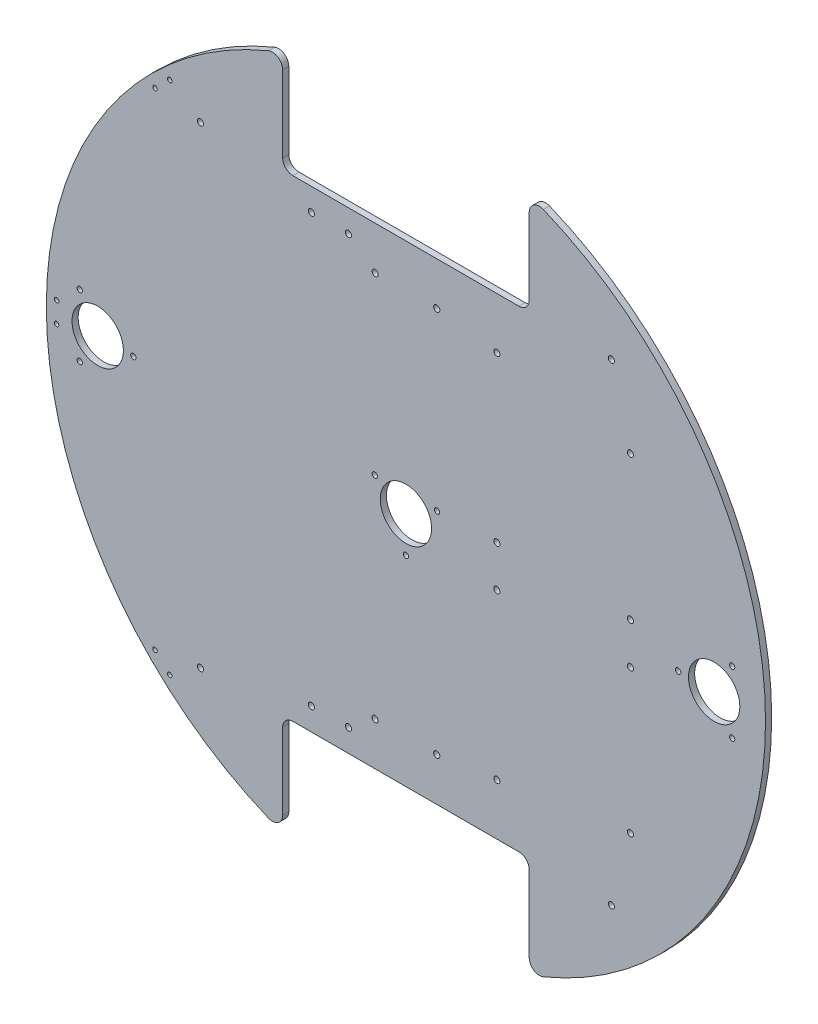
SolidWorks part; units mm, degrees
material "ｱｸﾘﾙ (中-上級の耐衝撃性)"
ref_plane "正面" through (0, 0, 0) normal (0, 0, 1) x (1, 0, 0)
ref_plane "平面" through (0, 0, 0) normal (0, 1, 0) x (1, 0, 0)
ref_plane "右側面" through (0, 0, 0) normal (1, 0, 0) x (0, 0, -1)
sketch "ｽｹｯﾁ1" plane through (0, 0, 0) normal (0, 0, 1) x (1, 0, 0)
  circle A0 centre (0, 0) radius 175
  dimension "D1" = 350
extrude "ﾎﾞｽ - 押し出し1" add sketch "ｽｹｯﾁ1" along normal blind 3
sketch "ｽｹｯﾁ2" plane through (0, 0, 3) normal (0, 0, 1) x (1, 0, 0)
  line L0 (0, 0) -> (175, 0)
  line L1 (0, 0) -> (-175, 0)
  line L2 (0, 0) -> (0, 115)
  line L3 (0, 0) -> (0, -115)
  line L4 (0, 115) -> (60, 115)
  line L5 (0, 115) -> (0, 175)
  line L6 (0, 175) -> (60, 175)
  line L7 (60, 115) -> (60, 175)
  line L8 (0, 115) -> (-60, 115)
  line L9 (0, 115) -> (0, 175)
  line L10 (0, 175) -> (-60, 175)
  line L11 (-60, 115) -> (-60, 175)
  line L13 (0, -115) -> (60, -115)
  line L14 (0, -115) -> (0, -175)
  line L15 (0, -175) -> (60, -175)
  line L16 (60, -115) -> (60, -175)
  line L17 (0, -115) -> (-60, -115)
  line L18 (0, -115) -> (0, -175)
  line L19 (0, -175) -> (-60, -175)
  line L20 (-60, -115) -> (-60, -175)
  circle A0 centre (0, 0) radius 175 construction
  circle M1 centre (0, 0) radius 175
  dimension "D1" = 115
  dimension "D2" = 60
  dimension "D3" = 60
  dimension "D4" = 60
  dimension "D5" = 115
  dimension "D6" = 60
extrude "ｶｯﾄ - 押し出し1" cut sketch "ｽｹｯﾁ2" against normal blind 3 contours L11 L8 L5 M1 | L4 L7 L5 M1 | L17 L20 L14 M1 | L16 L13 L14 M1
fillet "ﾌｨﾚｯﾄ1" radius 5 1 edges at (-60, 164.3928, 1.5)
fillet "ﾌｨﾚｯﾄ2" radius 5 3 edges at (60, 115, 1.5) (60, 164.3928, 1.5) (-60, 115, 1.5)
fillet "ﾌｨﾚｯﾄ3" radius 5 4 edges at (-60, -164.3928, 1.5) (-60, -115, 1.5) (60, -164.3928, 1.5) (60, -115, 1.5)
sketch "ｽｹｯﾁ5" plane through (0, 0, 3) normal (0, 0, 1) x (1, 0, 0)
  line L0 (0, 115) -> (-100, 115)
  line L1 (55, 115) -> (-55, 115) construction
  line L2 (0, 115) -> (100, 115)
  line L3 (0, -115) -> (100, -115)
  line L4 (55, -115) -> (-55, -115) construction
  line L5 (100, -115) -> (-100, -115)
  circle A0 centre (-100, -115) radius 1.5
  circle A1 centre (100, -115) radius 1.5
  circle A2 centre (100, 115) radius 1.5
  circle A3 centre (-100, 115) radius 1.5
  dimension "D3" = 3
  dimension "D4" = 3
  dimension "D5" = 3
  dimension "D6" = 3
  dimension "D1" = 100
  dimension "D2" = 100
extrude "ｶｯﾄ - 押し出し4" cut sketch "ｽｹｯﾁ5" against normal blind 3 contours A1 | A0 | A3 | A2
sketch "ｽｹｯﾁ10" plane through (0, 0, 3) normal (0, 0, 1) x (1, 0, 0)
  line L0 (0, 0) -> (-150, 0)
  line L1 (0, 0) -> (150, 0)
  line L2 (-150, 0) -> (-158.75, 15.1554)
  line L3 (-150, 0) -> (-158.75, -15.1554)
  line L4 (-150, 0) -> (-132.6329, 0)
  line L5 (0, 0) -> (15.1554, 8.75)
  line L6 (0, 0) -> (-15.1554, 8.75)
  line L7 (0, 0) -> (0, -17.5)
  line L8 (150, 0) -> (158.75, 15.1554)
  line L9 (150, 0) -> (132.5, 0)
  line L10 (150, 0) -> (158.75, -15.1554)
  circle A0 centre (-150, 0) radius 12.5
  circle A1 centre (150, 0) radius 12.5
  circle A2 centre (0, 0) radius 12.5
  circle A3 centre (-150, 0) radius 17.5
  circle A4 centre (0, 0) radius 17.5
  circle A5 centre (150, 0) radius 17.5
  circle A6 centre (132.5, 0) radius 1.3
  circle A7 centre (158.75, 15.1554) radius 1.3
  circle A8 centre (158.75, -15.1554) radius 1.3
  circle A9 centre (-15.1554, 8.75) radius 1.3
  circle A10 centre (15.1554, 8.75) radius 1.3
  circle A11 centre (0, -17.5) radius 1.3
  circle A12 centre (-158.75, 15.1554) radius 1.3
  circle A13 centre (-158.75, -15.1554) radius 1.3
  circle A14 centre (-132.6329, 0) radius 1.3
  dimension "D3" = 25
  dimension "D4" = 25
  dimension "D5" = 25
  dimension "D6" = 35
  dimension "D7" = 35
  dimension "D8" = 35
  dimension "D15" = 2.6
  dimension "D16" = 2.6
  dimension "D17" = 2.6
  dimension "D18" = 2.6
  dimension "D19" = 2.6
  dimension "D20" = 2.6
  dimension "D21" = 2.6
  dimension "D22" = 2.6
  dimension "D23" = 2.6
  dimension "D1" = 150
  dimension "D2" = 150
  dimension "D9" = 120
  dimension "D10" = 120
  dimension "D11" = 120
  dimension "D12" = 120
  dimension "D13" = 120
  dimension "D14" = 120
sketch "ｽｹｯﾁ12" plane through (0, 0, 3) normal (0, 0, 1) x (1, 0, 0)
  line L0 (0, 115) -> (0, 94)
  line L1 (55, 115) -> (-55, 115) construction
  line L2 (0, 94) -> (15, 94)
  line L3 (0, 94) -> (-15, 94)
  line L7 (0, -115) -> (0, -94)
  line L8 (55, -115) -> (-55, -115) construction
  line L9 (0, -94) -> (15, -94)
  line L10 (0, -94) -> (-15, -94)
  circle A0 centre (-15, 94) radius 1.5
  circle A1 centre (15, 94) radius 1.5
  circle A6 centre (-15, -94) radius 1.5
  circle A7 centre (15, -94) radius 1.5
  dimension "D5" = 3
  dimension "D6" = 3
  dimension "D7" = 15
  dimension "D13" = 3
  dimension "D14" = 3
  dimension "D1" = 21
  dimension "D2" = 15
  dimension "D3" = 15
  dimension "D4" = 15
  dimension "D9" = 21
sketch "ｽｹｯﾁ13" plane through (0, 0, 3) normal (0, 0, 1) x (1, 0, 0)
  line L0 (0, -115) -> (-25, -115)
  line L1 (55, -115) -> (-55, -115) construction
  line L2 (-25, -115) -> (-25, -104)
  line L3 (-46, 104) -> (-28, 104)
  line L4 (0, 115) -> (-28, 115)
  line L5 (-28, -104) -> (-46, -104)
  line L6 (-28, 104) -> (-27.8272, 103.8289)
  line L7 (0, 115) -> (0, -115)
  line L9 (55, 115) -> (-55, 115) construction
  line L10 (-28, 115) -> (-28, 104)
  line L12 (-28, 104) -> (-46, 104)
  circle A1 centre (-28, -104) radius 1.5
  circle A2 centre (-46, -104) radius 1.5
  circle A4 centre (-46, 104) radius 1.5
  circle A7 centre (-28, 104) radius 1.5
  dimension "D8" = 3
  dimension "D9" = 3
  dimension "D13" = 3
  dimension "D14" = 3
  dimension "D1" = 25
  dimension "D2" = 11
  dimension "D3" = 3
  dimension "D4" = 18
  dimension "D5" = 18
  dimension "D10" = 28
  dimension "D11" = 11
extrude "ｶｯﾄ - 押し出し13" cut sketch "ｽｹｯﾁ10" against normal blind 10 contours A12 | A0 | A13 | A14 | A2 | A9 | A10 | A11 | A6 | A1 | A7 | A8
sketch "ｽｹｯﾁ14" plane through (0, 0, 3) normal (0, 0, 1) x (1, 0, 0)
  line L0 (0, 0) -> (-170, 0)
  line L1 (-170, 0) -> (-170, 5)
  line L2 (-170, 0) -> (-170, -5)
  line L3 (0, 0) -> (-118.5181, 121.8748)
  line L4 (0, 0) -> (-118.5181, -121.8748)
  line L5 (-118.5181, 121.8748) -> (-114.9335, 125.3606)
  line L6 (-118.5181, 121.8748) -> (-122.1026, 118.389)
  line L7 (-118.5181, -121.8748) -> (-122.1026, -118.389)
  line L8 (-118.5181, -121.8748) -> (-114.9335, -125.3606)
  circle A0 centre (-170, 5) radius 1.1
  circle A1 centre (-170, -5) radius 1.1
  circle A2 centre (-114.9335, 125.3606) radius 1.1
  circle A3 centre (-122.1026, 118.389) radius 1.1
  circle A4 centre (-122.1026, -118.389) radius 1.1
  circle A5 centre (-114.9335, -125.3606) radius 1.1
  dimension "D4" = 2.2
  dimension "D5" = 2.2
  dimension "D14" = 2.2
  dimension "D15" = 2.2
  dimension "D16" = 2.2
  dimension "D17" = 2.2
  dimension "D1" = 170
  dimension "D2" = 5
  dimension "D3" = 5
  dimension "D6" = 45.8
  dimension "D7" = 45.8
  dimension "D8" = 170
  dimension "D9" = 170
  dimension "D10" = 5
  dimension "D11" = 5
  dimension "D12" = 5
  dimension "D13" = 5
extrude "ｶｯﾄ - 押し出し14" cut sketch "ｽｹｯﾁ14" against normal blind 10 contours A4 | A5 | A0 | A1 | A2 | A3
extrude "ｶｯﾄ - 押し出し17" cut sketch "ｽｹｯﾁ12" against normal blind 10 contours A6 | A7 | A0 | A1
extrude "ｶｯﾄ - 押し出し18" cut sketch "ｽｹｯﾁ13" against normal blind 5 contours A2 | A1 | A4 | A7
sketch "ｽｹｯﾁ15" plane through (0, 0, 3) normal (0, 0, 1) x (1, 0, 0)
  line L0 (12.5, 0) -> (131.2, 0) construction
  circle A0 centre (0, 0) radius 12.5 construction
  circle A1 centre (132.5, 0) radius 1.3 construction
  circle A2 centre (44.253, 10) radius 1.5
  circle A3 centre (44.253, 90) radius 1.5
  circle A4 centre (109.253, 10) radius 1.5
  circle A5 centre (109.253, 80) radius 1.5
  circle A6 centre (44.253, -10) radius 1.5
  circle A7 centre (109.253, -10) radius 1.5
  circle A8 centre (44.253, -90) radius 1.5
  circle A9 centre (109.253, -80) radius 1.5
  dimension "D1" = 3
  dimension "D2" = 10
  dimension "D3" = 3
  dimension "D4" = 80
  dimension "D5" = 3
  dimension "D6" = 65
  dimension "D7" = 3
  dimension "D8" = 70
  dimension "D10" = 3
  dimension "D11" = 3
  dimension "D12" = 65
  dimension "D13" = 3
  dimension "D14" = 80
  dimension "D15" = 3
  dimension "D16" = 70
extrude "ｶｯﾄ - 押し出し19" cut sketch "ｽｹｯﾁ15" against normal through all
